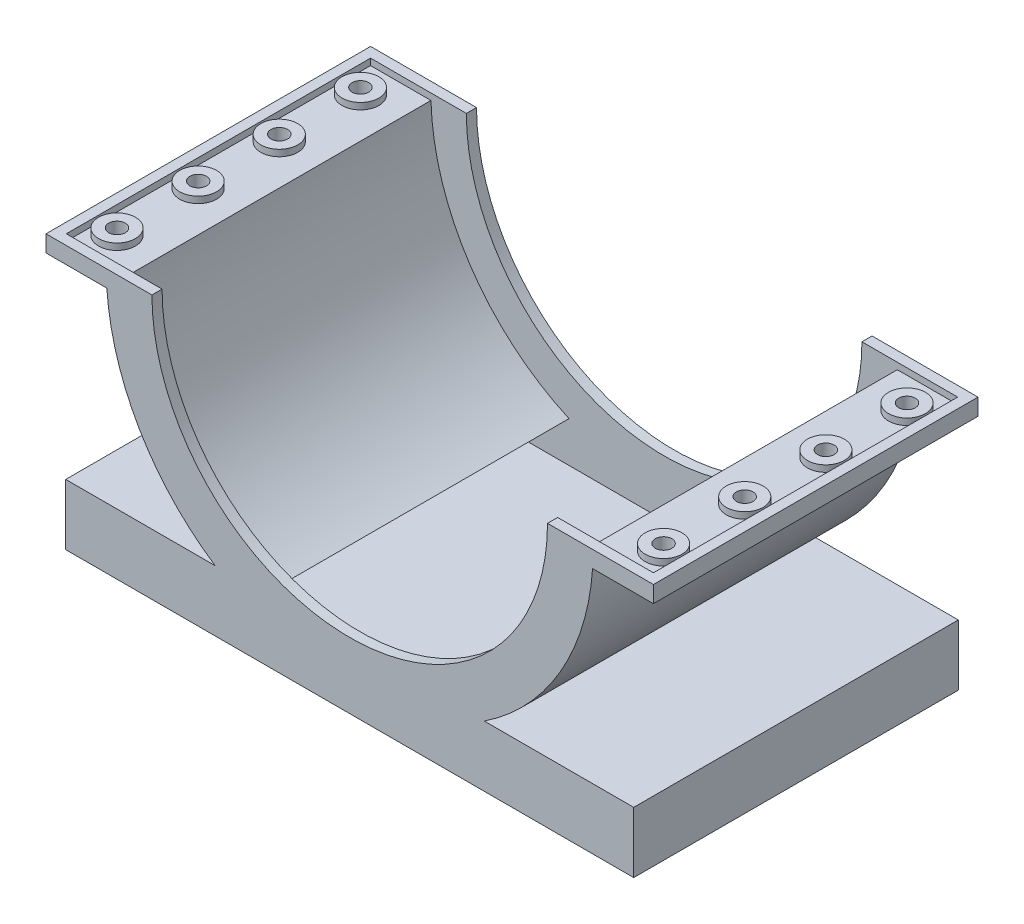
SolidWorks part; units mm, degrees
ref_plane "Front Plane" through (0, 0, 0) normal (0, 0, 1) x (1, 0, 0)
ref_plane "Top Plane" through (0, 0, 0) normal (0, 1, 0) x (1, 0, 0)
ref_plane "Right Plane" through (0, 0, 0) normal (1, 0, 0) x (0, 0, -1)
sketch "Sketch1" plane through (0, 0, 0) normal (0, 0, 1) x (1, 0, 0)
  line L0 (-7.486, 0) -> (-4.875, 0)
  line L1 (-7.486, -0.41) -> (-5.986, -0.41)
  line L2 (-7, -5) -> (-3.3166, -5)
  line L3 (-7, -5) -> (-7, -6.5)
  line L4 (-7, -6.5) -> (7, -6.5)
  line L5 (7, -5) -> (7, -6.5)
  line L6 (7.486, 0) -> (7.486, -0.41)
  line L7 (5.986, -0.41) -> (7.486, -0.41)
  line L8 (-8.145, -0.41) -> (9.3803, -0.41) construction
  line L9 (4.875, 0) -> (7.486, 0)
  line L10 (-7.486, 0) -> (-7.486, -0.41)
  line L11 (-8.145, 0) -> (9.3803, 0) construction
  line L12 (3.3166, -5) -> (7, -5)
  arc A1 (-5.986, -0.41) -> (-3.3166, -5) centre (0, 0) ccw
  arc A2 (3.3166, -5) -> (5.986, -0.41) centre (0, 0) ccw
  arc A3 (-4.875, 0) -> (4.875, 0) centre (0, 0) ccw
  point P11 (0, -6.5)
  dimension "D2" = 12
  dimension "D3" = 4.875
  dimension "D4" = 1.5
  dimension "D5" = 5
  dimension "D6" = 14
  dimension "D8" = 1.5
  dimension "D9" = 1.5
  dimension "D7" = 0.41
extrude "Boss-Extrude2" add sketch "Sketch1" along normal mid plane 8
sketch "Sketch3" plane through (0, 0, 0) normal (0, 1, 0) x (1, 0, 0)
  line L0 (-4.875, -4) -> (-7.486, -4) construction
  line L1 (-7.486, -4) -> (-7.486, 4) construction
  line L2 (0, 5.3567) -> (0, -4.7789) construction
  circle A0 centre (-6.736, 3) radius 0.205
  circle A1 centre (-6.736, 1) radius 0.205
  circle A2 centre (-6.736, -1) radius 0.205
  circle A3 centre (-6.736, -3) radius 0.205
  circle A4 centre (6.736, -3) radius 0.205
  circle A5 centre (6.736, -1) radius 0.205
  circle A6 centre (6.736, 1) radius 0.205
  circle A7 centre (6.736, 3) radius 0.205
  dimension "D1" = 1
  dimension "D3" = 0.41
  dimension "D2" = 0.75
  dimension "D4" = 2
  dimension "D5" = 2
  dimension "D6" = 2
extrude "Cut-Extrude2" cut sketch "Sketch3" against normal up to next
shell "Shell1" thickness 0.25
